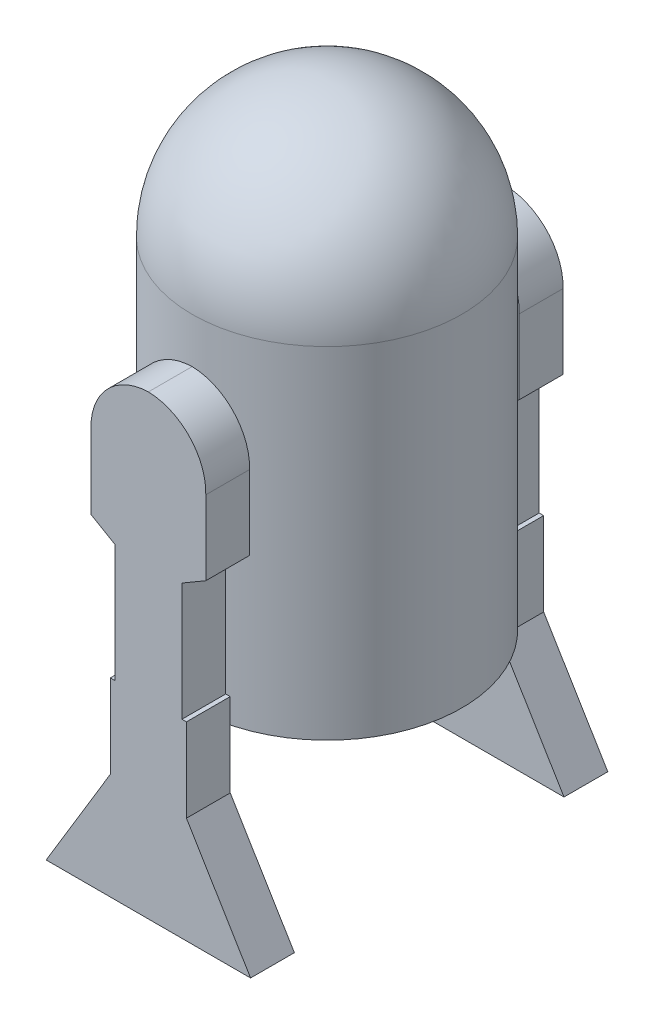
SolidWorks part; units mm, degrees
ref_plane "Front Plane" through (0, 0, 0) normal (0, 0, 1) x (1, 0, 0)
ref_plane "Top Plane" through (0, 0, 0) normal (0, 1, 0) x (1, 0, 0)
ref_plane "Right Plane" through (0, 0, 0) normal (1, 0, 0) x (0, 0, -1)
sketch "Sketch1" plane through (0, 0, 0) normal (1, 0, 0) x (0, 0, -1)
  line L0 (0, 0) -> (0, 1090) construction
  line L1 (169.5839, 929.2257) -> (836.2506, 929.2257) construction
  line L2 (0, 786.7671) -> (230.8699, 786.7671)
  line L3 (230.8699, 786.7671) -> (230.8699, 278.0283)
  line L6 (230.8699, 278.0283) -> (169.9887, 278.0283)
  line L7 (169.9887, 278.0283) -> (132.0677, 219.1896)
  line L8 (132.0677, 219.1896) -> (0, 219.1896)
  line L9 (0, 219.1896) -> (0, 786.7671)
revolve "Revolve1" add sketch "Sketch1" angle 360 about L9
sketch "Sketch2" plane through (0, 0, 0) normal (1, 0, 0) x (0, 0, -1)
  line L0 (95.817, 929.7543) -> (762.4837, 929.7543) construction
  line L5 (-230.8699, 786.7671) -> (-230.8699, 861.7671)
  line L6 (0, 786.7671) -> (0, 1092.637)
  line L7 (230.8699, 786.7671) -> (-230.8699, 786.7671) construction
  line L8 (-230.8699, 786.7671) -> (0, 786.7671)
  line L9 (-230.8699, 786.7671) -> (0, 786.7671)
  line L10 (0, 786.7671) -> (0, 742.3952) construction
  arc A1 (-230.8699, 861.7671) -> (0, 1092.637) centre (0, 861.7671) cw
revolve "Revolve3" add sketch "Sketch2" angle 360 about L10
ref_plane "Plane1" through (0, 0, -230.8699) normal (0, 0, -1) x (-1, 0, 0)
sketch "Sketch6" plane through (0, 0, 0) normal (1, 0, 0) x (0, 0, -1)
  line L0 (-440.1715, 1005.1666) -> (226.4951, 1005.1666) construction
  line L1 (230.8699, 784.3764) -> (310.4814, 784.3764)
  line L2 (230.8699, 278.0283) -> (230.8699, 861.7671) construction
  line L3 (310.4814, 784.3764) -> (310.4814, 342.2186)
  line L4 (310.4814, 342.2186) -> (310.4814, 336.2466)
  line L5 (310.4814, 336.2466) -> (321.7304, 336.2466)
  line L6 (321.7304, 336.2466) -> (321.7304, 324.7417)
  line L7 (321.7304, 324.7417) -> (316.1059, 324.7417)
  line L8 (316.1059, 324.7417) -> (316.1059, 278.8565)
  line L9 (316.1059, 278.8565) -> (286.6251, 227.4981)
  line L10 (286.6251, 227.4981) -> (286.6251, 166.4743)
  line L11 (286.6251, 166.4743) -> (301.3655, 166.4743)
  line L12 (301.3655, 166.4743) -> (362.8093, -10.2798)
  line L13 (362.8093, -10.2798) -> (166.2058, -10.2798)
  line L14 (166.2058, -10.2798) -> (166.2058, 16.7679)
sketch "Sketch7" plane through (0, 0, -230.8699) normal (0, 0, -1) x (-1, 0, 0)
  line L0 (-754.2902, 799.6279) -> (-87.6235, 799.6279) construction
  line L1 (0, 1092.637) -> (286.0173, 1092.637) construction
  line L2 (286.0173, 1092.637) -> (286.0173, 2.637) construction
  line L3 (-527.558, 621.7251) -> (139.1086, 621.7251) construction
  line L4 (286.0173, 2.637) -> (-251.447, 2.637) construction
  line L5 (-734.6047, 781.6628) -> (-67.938, 781.6628) construction
  line L6 (0, 680.8319) -> (98.3028, 680.8319) construction
  line L7 (0, 784.3764) -> (0, 342.2186) construction
  line L8 (98.3028, 680.8319) -> (98.3028, 553.4653)
  line L9 (98.3028, 553.4653) -> (57.4431, 529.5952)
  line L10 (57.4431, 529.5952) -> (57.4431, 327.576)
  line L11 (57.4431, 327.576) -> (65.1517, 327.576)
  line L12 (65.1517, 327.576) -> (65.1517, 184.6846)
  line L13 (0, 2.637) -> (0, 680.8319) construction
  line L15 (-175, 2.637) -> (175, 2.637)
  line L16 (0, 166.4743) -> (0, -10.2798) construction
  line L17 (175, 2.637) -> (65.1517, 184.6846)
  line L18 (0, 680.8319) -> (0, 784.3764) construction
  line L19 (-65.1517, 327.576) -> (-65.1517, 184.6846)
  line L20 (-57.4431, 327.576) -> (-65.1517, 327.576)
  line L21 (-57.4431, 529.5952) -> (-57.4431, 327.576)
  line L22 (-98.3028, 553.4653) -> (-57.4431, 529.5952)
  line L23 (-98.3028, 680.8319) -> (-98.3028, 553.4653)
  line L24 (-175, 2.637) -> (-65.1517, 184.6846)
  arc A0 (230.8699, 861.7671) -> (-230.8699, 861.7671) centre (0, 861.7671) ccw construction
  arc A1 (98.3028, 680.8319) -> (0, 784.3764) centre (-2.6208, 683.4527) ccw
  arc A2 (-98.3028, 680.8319) -> (0, 784.3764) centre (2.6208, 683.4527) cw
extrude "Boss-Extrude1" add sketch "Sketch7" along normal blind 75 separate body
mirror "Mirror18" about plane through (0, 0, 0) normal (0, 0, 1) of bodies 103
